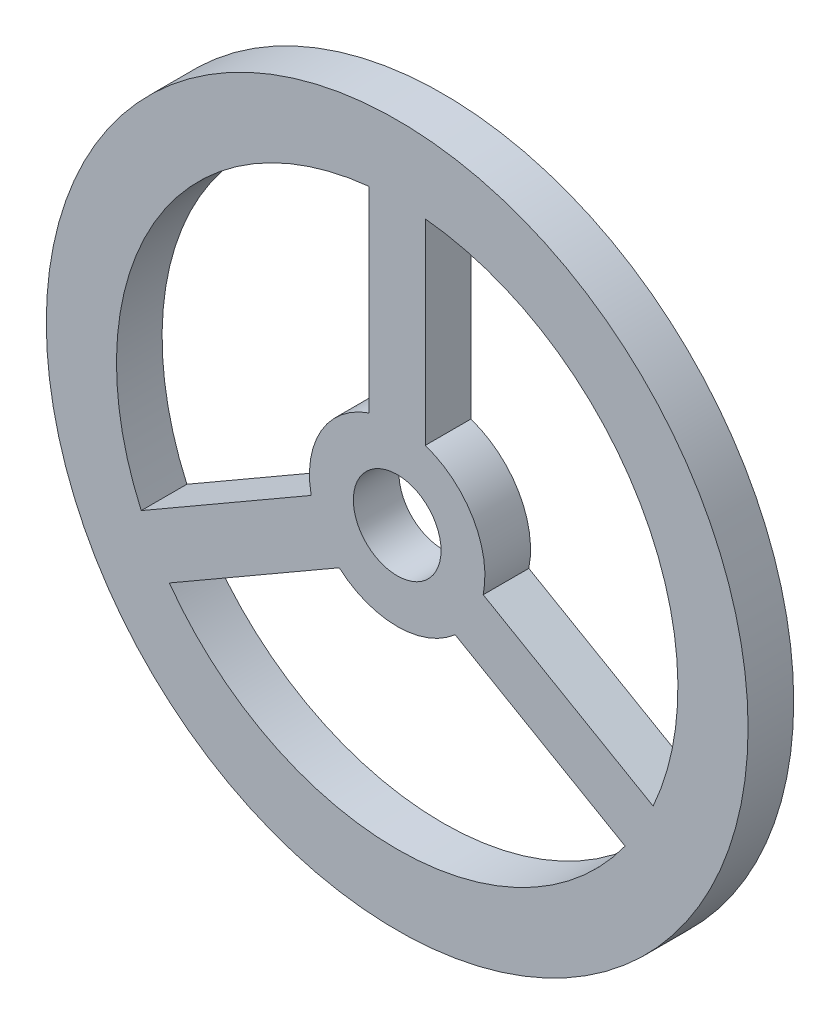
SolidWorks part; units mm, degrees
ref_plane "Plan de face" through (0, 0, 0) normal (0, 0, 1) x (1, 0, 0)
ref_plane "Plan de dessus" through (0, 0, 0) normal (0, 1, 0) x (1, 0, 0)
ref_plane "Plan de droite" through (0, 0, 0) normal (1, 0, 0) x (0, 0, -1)
sketch "Esquisse1" plane through (0, 0, 0) normal (0, 0, 1) x (1, 0, 0)
  circle A0 centre (0, 0) radius 10
  dimension "D1" = 20
extrude "Boss.-Extru.1" add sketch "Esquisse1" along normal blind 1.3
sketch "Esquisse2" plane through (0, 0, 1.3) normal (0, 0, 1) x (1, 0, 0)
  line L0 (0, 0) -> (0, 18.3538) construction
  line L1 (0, 0) -> (-19.6307, -11.3338) construction
  line L2 (0, 0) -> (15.8132, -9.1297) construction
  line L3 (-19.8178, -10.5181) -> (3.9669, 3.2141) construction
  line L4 (-19.39, -12.1186) -> (5.1103, 2.0267) construction
  line L5 (-7.2935, -3.2871) -> (-2.4512, -0.4915)
  line L6 (-6.4935, -4.6728) -> (-1.6512, -1.8771)
  line L7 (0.7488, -1.3561) -> (9.8788, -6.6273) construction
  line L8 (11.2016, -5.5435) -> (2.0009, -0.2315) construction
  line L9 (6.4935, -4.6728) -> (1.6512, -1.8771)
  line L10 (2.4512, -0.4915) -> (7.2935, -3.2871)
  line L11 (0.8, 14.5591) -> (0.8, 1.7887) construction
  line L12 (-0.8, 1.7923) -> (-0.8, 14.4293) construction
  line L13 (-0.8, 7.9599) -> (-0.8, 2.3685)
  line L14 (0.8, 2.3685) -> (0.8, 7.9599)
  arc A0 (-6.4935, -4.6728) -> (6.4935, -4.6728) centre (0, 0) ccw
  arc A1 (-1.6512, -1.8771) -> (1.6512, -1.8771) centre (0, 0) ccw
  arc A2 (2.4512, -0.4915) -> (0.8, 2.3685) centre (0, 0) ccw
  arc A3 (7.2935, -3.2871) -> (0.8, 7.9599) centre (0, 0) ccw
  arc A4 (-0.8, 7.9599) -> (-7.2935, -3.2871) centre (0, 0) ccw
  arc A5 (-0.8, 2.3685) -> (-2.4512, -0.4915) centre (0, 0) ccw
  dimension "D1" = 120
  dimension "D2" = 120
  dimension "D3" = 0.8
  dimension "D4" = 0.8
  dimension "D5" = 0.8
  dimension "D6" = 0.8
  dimension "D7" = 0.8
  dimension "D8" = 0.8
extrude "Enlèv. mat.-Extru.1" cut sketch "Esquisse2" against normal through all
sketch "Esquisse3" plane through (0, 0, 1.3) normal (0, 0, 1) x (1, 0, 0)
  circle A0 centre (0, 0) radius 1.25
  dimension "D1" = 2.5
extrude "Enlèv. mat.-Extru.2" cut sketch "Esquisse3" against normal through all
